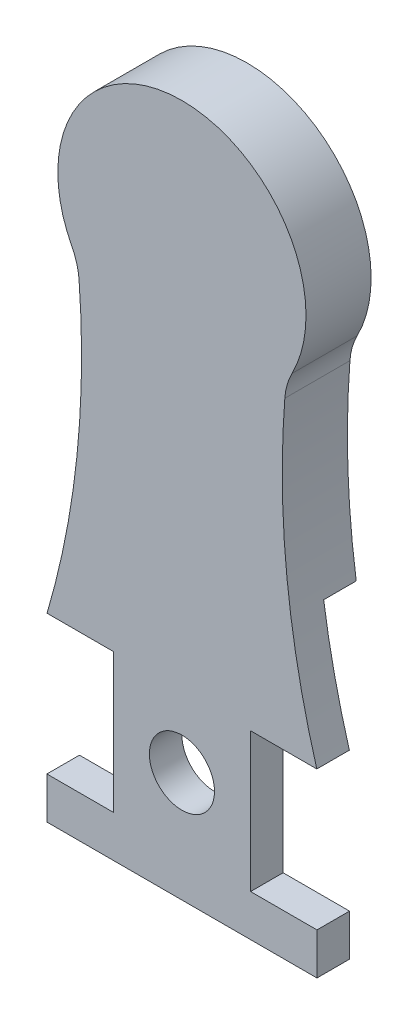
SolidWorks part; units mm, degrees
ref_plane "Front Plane" through (0, 0, 0) normal (0, 0, 1) x (1, 0, 0)
ref_plane "Top Plane" through (0, 0, 0) normal (0, 1, 0) x (1, 0, 0)
ref_plane "Right Plane" through (0, 0, 0) normal (1, 0, 0) x (0, 0, -1)
sketch "Sketch1" plane through (0, 0, 0) normal (0, 0, 1) x (1, 0, 0)
  line L0 (0, 0) -> (0, 60) construction
  line L1 (-53.033, -53.033) -> (0, 0) construction
  line L2 (0, 60) -> (16, 60) construction
  line L3 (0, 60) -> (0, 50) construction
  line L4 (0, 60) -> (-16, 60) construction
  line L5 (0, 0) -> (0, -95.7808) construction
  line L6 (0, 0) -> (53.033, -53.033) construction
  line L8 (-64.561, -58.9899) -> (67.8775, -58.9899) construction
  line L9 (-20.9932, 10.8458) -> (-10.5429, 10.8458) construction
  line L10 (-10.5429, 10.8458) -> (-10.5429, -10.5429) construction
  line L11 (-10.5429, -10.5429) -> (-20.7412, -10.5429) construction
  line L12 (-20.7412, -10.5429) -> (-20.7412, -16.9424) construction
  line L13 (20.7412, -10.5429) -> (20.7412, -16.9424) construction
  line L14 (10.5429, -10.5429) -> (20.7412, -10.5429) construction
  line L15 (10.5429, 10.8458) -> (10.5429, -10.5429) construction
  line L16 (20.9932, 10.8458) -> (10.5429, 10.8458) construction
  line L17 (-20.7412, -16.9424) -> (20.7412, -16.9424) construction
  line L18 (-63.2289, -53.033) -> (63.2289, -53.033) construction
  line L19 (0, 0) -> (-57.4533, -48.2091) construction
  line L20 (0, 0) -> (57.4533, -48.2091) construction
  circle A0 centre (0, 0) radius 5 construction
  arc A1 (-57.4533, -48.2091) -> (-16, 60) centre (-145.6998, 47.6415) ccw
  arc A2 (57.4533, -48.2091) -> (16, 60) centre (145.6998, 47.6415) cw
  arc A3 (-16, 60) -> (16, 60) centre (0, 70.3554) cw
  arc A5 (57.4533, -48.2091) -> (-57.4533, -48.2091) centre (0, 0) cw
  point P20 (0, -106.066)
  dimension "D1" = 10
  dimension "D2" = 75
  dimension "D3" = 60
  dimension "D4" = 5
  dimension "D5" = 5
  dimension "D6" = 41.4824
  dimension "D7" = 21.3887
  dimension "D8" = 6.3996
  dimension "D9" = 21.0858
  dimension "D10" = 6.3995
extrude "Body" add sketch "Sketch1" along normal blind 10
sketch "Sketch2" plane through (0, 0, 10) normal (0, 0, 1) x (1, 0, 0)
  circle A0 centre (0, 0) radius 5
  dimension "D1" = 10
extrude "Attachment Hole" cut sketch "Sketch2" against normal through all
sketch "Sketch17" plane through (0, 0, 10) normal (0, 0, 1) x (1, 0, 0)
  line L0 (-20.9932, 10.8458) -> (-10.5429, 10.8458)
  line L1 (-10.5429, 10.8458) -> (-10.5429, -10.5429)
  line L2 (-10.5429, -10.5429) -> (-20.7412, -10.5429)
  line L3 (-20.7412, -10.5429) -> (-20.7412, -16.9424)
  line L4 (-20.7412, -16.9424) -> (20.7412, -16.9424)
  line L5 (20.7412, -16.9424) -> (20.7412, -10.5429)
  line L6 (20.7412, -10.5429) -> (10.5429, -10.5429)
  line L7 (10.5429, -10.5429) -> (10.5429, 10.8458)
  line L8 (10.5429, 10.8458) -> (20.9932, 10.8458)
  line L9 (0, 0) -> (0, 42.2888) construction
  line L10 (0, 0) -> (0, 60) construction
  line L11 (0, 36.1313) -> (0, -16.9424) construction
  arc A0 (-20.9932, 10.8458) -> (-16.8596, 28.2771) centre (-174.762, 56.5155) ccw
  arc A1 (-57.4533, -48.2091) -> (-16, 60) centre (-145.6998, 47.6415) ccw construction
  arc A2 (20.9932, 10.8458) -> (16.8596, 28.2771) centre (174.762, 56.5155) cw
  arc A3 (-16.8596, 28.2771) -> (16.8596, 28.2771) centre (0, 14.1091) cw
  dimension "D1" = 53.0738
sketch "Sketch34" plane through (0, 0, 10) normal (0, 0, 1) x (1, 0, 0)
  line L0 (-20.9932, 10.8458) -> (-10.5429, 10.8458)
  line L1 (-10.5429, 10.8458) -> (-10.5429, -10.5429)
  line L2 (-10.5429, -10.5429) -> (-20.7412, -10.5429)
  line L3 (-20.7412, -10.5429) -> (-20.7412, -16.9424)
  line L4 (-20.7412, -16.9424) -> (20.7412, -16.9424)
  line L5 (20.7412, -16.9424) -> (20.7412, -10.5429)
  line L6 (20.7412, -10.5429) -> (10.5429, -10.5429)
  line L7 (10.5429, -10.5429) -> (10.5429, 10.8458)
  line L8 (10.5429, 10.8458) -> (20.9932, 10.8458)
  arc A0 (-20.9932, 10.8458) -> (-57.4533, -48.2091) centre (-148.4496, 48.754) cw
  arc A1 (-57.4533, -48.2091) -> (57.4533, -48.2091) centre (0, 0) ccw
  arc A2 (57.4533, -48.2091) -> (20.9932, 10.8458) centre (209.9801, 86.7426) cw
extrude "Cut-Extrude28" cut sketch "Sketch34" against normal through all
sketch "Sketch35" plane through (0, 0, 0) normal (0, 0, -1) x (-1, 0, 0)
  line L0 (20.9932, 10.8458) -> (10.5429, 10.8458)
  line L1 (10.5429, 10.8458) -> (10.5429, -10.5429)
  line L2 (10.5429, -10.5429) -> (20.7412, -10.5429)
  line L3 (20.7412, -10.5429) -> (20.7412, -16.9424)
  line L4 (20.7412, -16.9424) -> (-20.7412, -16.9424)
  line L5 (-20.7412, -16.9424) -> (-20.7412, -10.5429)
  line L6 (-20.7412, -10.5429) -> (-10.5429, -10.5429)
  line L7 (-10.5429, -10.5429) -> (-10.5429, 10.8458)
  line L8 (-10.5429, 10.8458) -> (-20.9932, 10.8458)
  arc A0 (-16.8596, 28.7771) -> (16.8596, 28.7771) centre (0, 14.6091) cw
  arc A1 (-20.9932, 10.8458) -> (-16.8596, 28.7771) centre (-178.7447, 56.6532) ccw
  arc A2 (16.8596, 28.7771) -> (20.9932, 10.8458) centre (154.8947, 51.1552) ccw
extrude "Cut-Extrude30" cut sketch "Sketch35" against normal blind 5
fillet "Fillet1" radius 10 1 edges at (16, 60, 5)
fillet "Fillet2" radius 10 1 edges at (-16, 60, 5)
